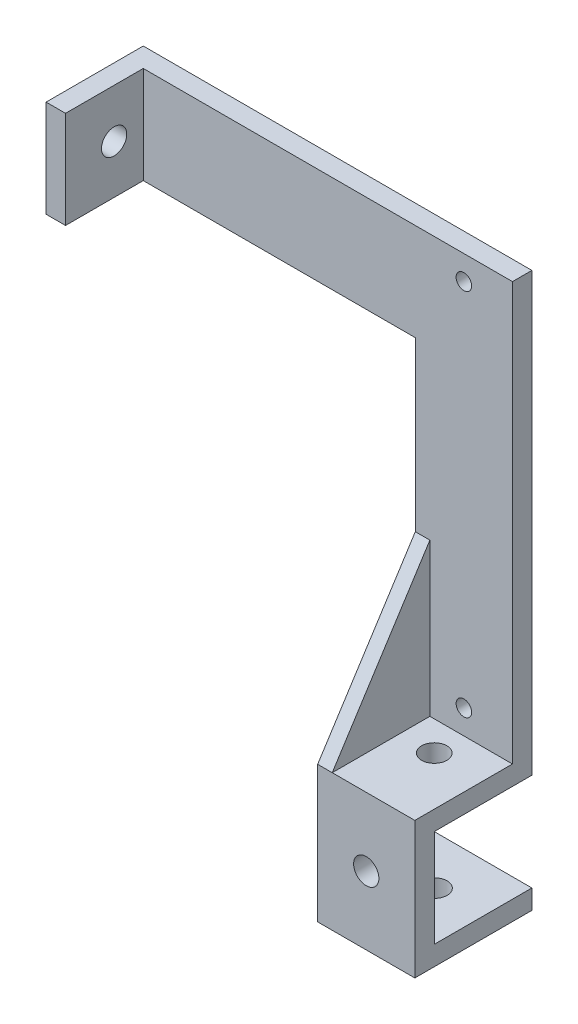
SolidWorks part; units mm, degrees
ref_plane "前视基准面" through (0, 0, 0) normal (0, 0, 1) x (1, 0, 0)
ref_plane "上视基准面" through (0, 0, 0) normal (0, 1, 0) x (1, 0, 0)
ref_plane "右视基准面" through (0, 0, 0) normal (1, 0, 0) x (0, 0, -1)
sketch "草图1" plane through (0, 0, 0) normal (0, 0, 1) x (1, 0, 0)
  line L1 (-9.2097, 42.7391) -> (-29.2097, 42.7391)
  line L2 (-9.2097, 42.7391) -> (-9.2097, -47.2609)
  line L3 (-9.2097, -47.2609) -> (-29.2097, -47.2609)
  line L4 (-29.2097, 42.7391) -> (-29.2097, -47.2609)
  dimension "D1" = 90
  dimension "D2" = 20
extrude "凸台-拉伸1" add sketch "草图1" along normal blind 4
sketch "草图2" plane through (0, 0, 4) normal (0, 0, 1) x (1, 0, 0)
  line L0 (-29.2097, -43.2609) -> (-9.2097, -43.2609)
  line L1 (-29.2097, 42.7391) -> (-29.2097, -47.2609) construction
  line L2 (-9.2097, -47.2609) -> (-9.2097, 42.7391) construction
  line L3 (-29.2097, -47.2609) -> (-9.2097, -47.2609) construction
  line L4 (-29.2097, -43.2609) -> (-29.2097, -47.2609)
  line L5 (-29.2097, -47.2609) -> (-9.2097, -47.2609)
  line L6 (-9.2097, -47.2609) -> (-9.2097, -43.2609)
  dimension "D1" = 4
extrude "凸台-拉伸2" add sketch "草图2" along normal blind 20.1
sketch "草图3" plane through (0, -47.2609, 0) normal (0, -1, 0) x (-1, 0, 0)
  line L0 (9.2097, -20.1) -> (29.2097, -20.1)
  line L1 (9.2097, -24.1) -> (9.2097, 0) construction
  line L2 (29.2097, -24.1) -> (29.2097, 0) construction
  line L3 (29.2097, -24.1) -> (9.2097, -24.1) construction
  line L4 (9.2097, -20.1) -> (9.2097, -24.1)
  line L5 (9.2097, -24.1) -> (29.2097, -24.1)
  line L6 (29.2097, -24.1) -> (29.2097, -20.1)
  dimension "D1" = 4
extrude "凸台-拉伸3" add sketch "草图3" along normal blind 24.1
sketch "草图4" plane through (0, 0, 20.1) normal (0, 0, -1) x (-1, 0, 0)
  line L0 (9.2097, -67.3609) -> (29.2097, -67.3609)
  line L1 (9.2097, -71.3609) -> (9.2097, -47.2609) construction
  line L2 (29.2097, -71.3609) -> (29.2097, -47.2609) construction
  line L3 (29.2097, -71.3609) -> (9.2097, -71.3609) construction
  line L4 (9.2097, -67.3609) -> (9.2097, -71.3609)
  line L5 (9.2097, -71.3609) -> (29.2097, -71.3609)
  line L6 (29.2097, -71.3609) -> (29.2097, -67.3609)
  dimension "D1" = 4
extrude "凸台-拉伸4" add sketch "草图4" along normal blind 20.1
sketch "草图5" plane through (0, -47.2609, 0) normal (0, -1, 0) x (-1, 0, 0)
  circle A0 centre (19.2097, -10.0948) radius 2.6
  dimension "D1" = 5.2
extrude "切除-拉伸1" cut sketch "草图5" against normal blind 20
sketch "草图6" plane through (0, 0, 20.1) normal (0, 0, -1) x (-1, 0, 0)
  circle A0 centre (19.2097, -57.3109) radius 2.6
  dimension "D1" = 5.2
extrude "切除-拉伸2" cut sketch "草图6" against normal blind 20
sketch "草图7" plane through (0, -67.3609, 0) normal (0, 1, 0) x (1, 0, 0)
  circle A0 centre (-19.2097, -10.05) radius 2.6
  dimension "D1" = 5.2
extrude "切除-拉伸3" cut sketch "草图7" against normal blind 20
sketch "草图9" plane through (0, 0, 0) normal (0, 0, -1) x (-1, 0, 0)
  circle A0 centre (19.2097, 37.7391) radius 1.6
  circle A1 centre (19.2097, -38.2609) radius 1.6
  dimension "D3" = 3.2
  dimension "D4" = 3.2
extrude "切除-拉伸4" cut sketch "草图9" against normal blind 20
sketch "草图10" plane through (-9.2097, 0, 0) normal (1, 0, 0) x (0, 0, -1)
  line L0 (-4, -11.8483) -> (-24.1, -43.2609)
  line L1 (-4, -43.2609) -> (-4, 42.7391) construction
sketch "草图12" plane through (0, 0, 4) normal (0, 0, 1) x (1, 0, 0)
  line L0 (-9.2097, -11.8483) -> (-29.2097, -11.8483)
  line L1 (-29.2097, 42.7391) -> (-29.2097, -43.2609) construction
  line L2 (-29.2097, 42.7391) -> (-29.2097, -47.2609) construction
sketch "草图13" plane through (-29.2097, 0, 0) normal (-1, 0, 0) x (0, 0, 1)
  line L0 (4, -11.8483) -> (24.1, -43.2609)
  line L1 (24.1, -43.2609) -> (4, -43.2609)
  line L2 (4, -43.2609) -> (4, -11.8483)
extrude "凸台-拉伸6" add sketch "草图13" against normal blind 3
sketch "草图14" plane through (-29.2097, 0, 0) normal (-1, 0, 0) x (0, 0, 1)
  line L0 (0, 22.7391) -> (4, 22.7391)
  line L1 (0, 42.7391) -> (0, -47.2609) construction
  line L2 (4, 42.7391) -> (4, -11.8483) construction
  line L3 (4, 42.7391) -> (0, 42.7391) construction
  line L4 (0, 42.7391) -> (0, 22.7391)
  line L5 (4, 22.7391) -> (4, 42.7391)
  line L6 (4, 42.7391) -> (0, 42.7391)
  dimension "D1" = 20
extrude "凸台-拉伸7" add sketch "草图14" along normal blind 60
sketch "草图15" plane through (0, 0, 4) normal (0, 0, 1) x (1, 0, 0)
  line L0 (-85.2097, 42.7391) -> (-85.2097, 22.7391)
  line L1 (-9.2097, 42.7391) -> (-89.2097, 42.7391) construction
  line L2 (-89.2097, 22.7391) -> (-29.2097, 22.7391) construction
  line L3 (-89.2097, 22.7391) -> (-89.2097, 42.7391) construction
  line L4 (-85.2097, 42.7391) -> (-89.2097, 42.7391)
  line L5 (-89.2097, 42.7391) -> (-89.2097, 22.7391)
  line L6 (-89.2097, 22.7391) -> (-85.2097, 22.7391)
  dimension "D1" = 4
extrude "凸台-拉伸8" add sketch "草图15" along normal blind 16
sketch "草图17" plane through (-89.2097, 0, 0) normal (-1, 0, 0) x (0, 0, 1)
  circle A0 centre (10, 32.7391) radius 2.6
  dimension "D1" = 5.2
extrude "切除-拉伸6" cut sketch "草图17" against normal blind 20
